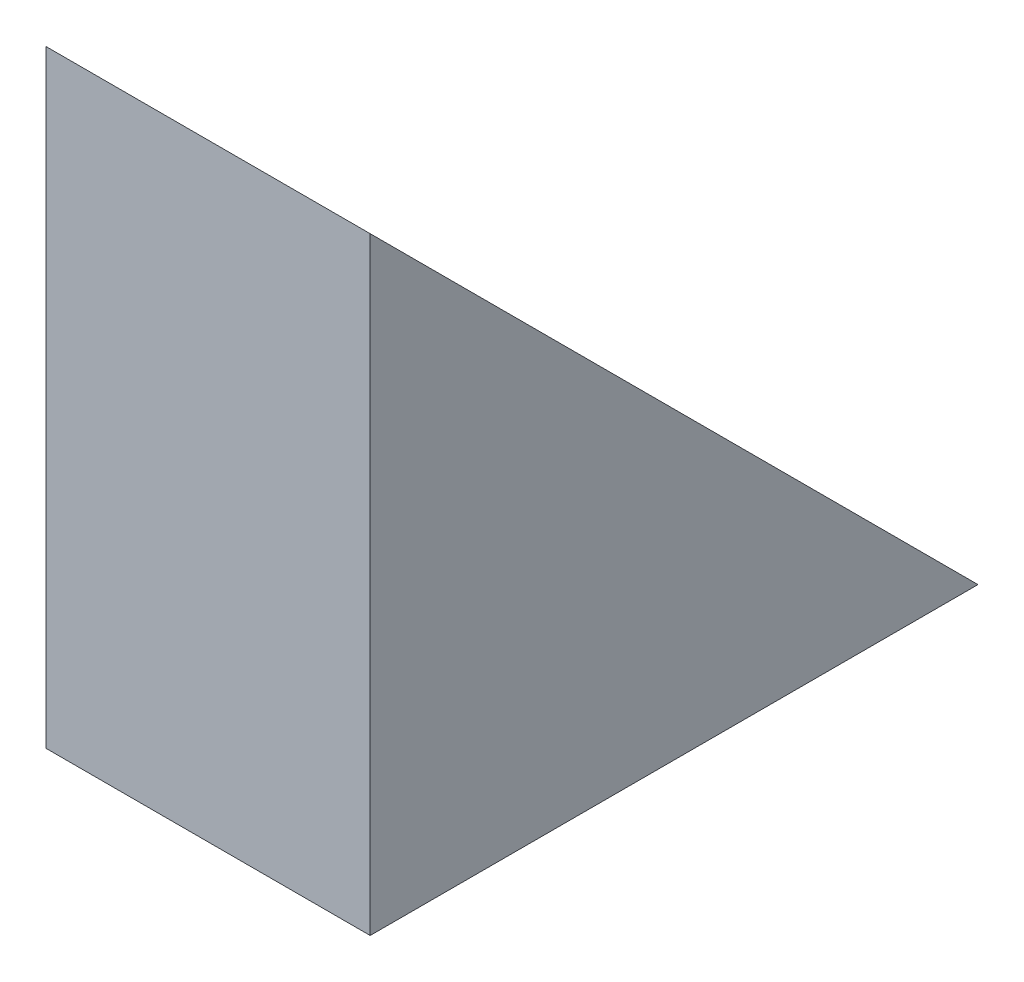
SolidWorks part; units mm, degrees
ref_plane "Ön Düzlem" through (0, 0, 0) normal (0, 0, 1) x (1, 0, 0)
ref_plane "Üst Düzlem" through (0, 0, 0) normal (0, 1, 0) x (1, 0, 0)
ref_plane "Sağ Düzlem" through (0, 0, 0) normal (1, 0, 0) x (0, 0, -1)
sketch "Çizim1" plane through (0, 0, 0) normal (1, 0, 0) x (0, 0, -1)
  line L0 (0, 150) -> (0, 0)
  line L1 (0, 0) -> (150, 0)
  line L2 (150, 0) -> (0, 150)
  dimension "D1" = 150
  dimension "D2" = 150
extrude "Yükseklik-Ekstrüzyon1" add sketch "Çizim1" against normal blind 80
